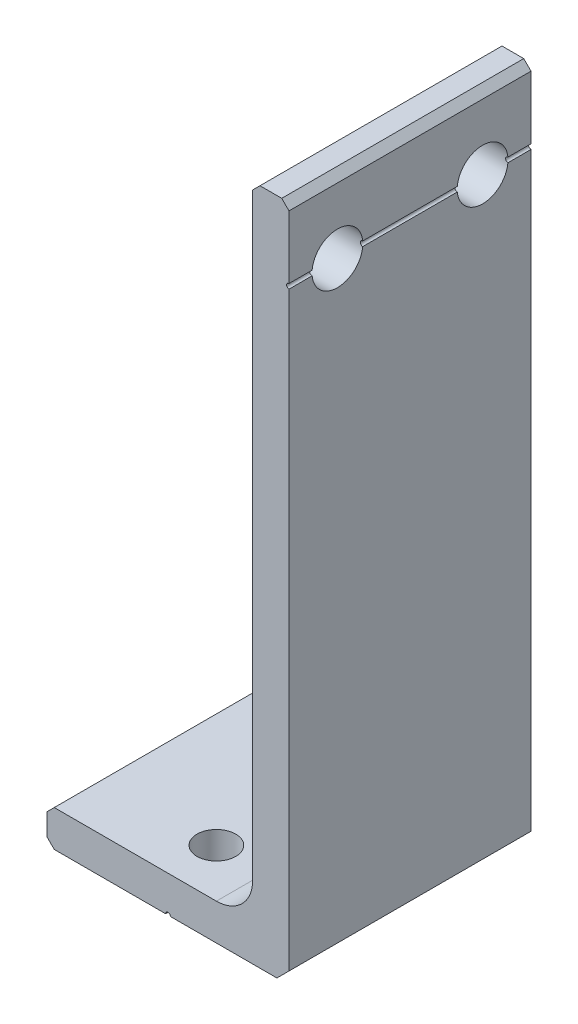
SolidWorks part; units mm, degrees
material "6061 合金"
ref_plane "前视基准面" through (0, 0, 0) normal (0, 0, 1) x (1, 0, 0)
ref_plane "上视基准面" through (0, 0, 0) normal (0, 1, 0) x (1, 0, 0)
ref_plane "右视基准面" through (0, 0, 0) normal (1, 0, 0) x (0, 0, -1)
sketch "草图1" plane through (0, 0, 0) normal (0, 0, 1) x (1, 0, 0)
  line L0 (0, 0) -> (20, 0)
  line L1 (20, 0) -> (20, 56)
  line L2 (20, 56) -> (17, 56)
  line L3 (17, 56) -> (17, 3)
  line L4 (17, 3) -> (0, 3)
  line L5 (0, 3) -> (0, 0)
  dimension "D1" = 3
  dimension "D2" = 53
  dimension "D3" = 3
  dimension "D4" = 20
extrude "凸台-拉伸1" add sketch "草图1" along normal blind 20
fillet "圆角1" radius 3 1 edges at (17, 3, 10)
sketch "草图2" plane through (17, 0, 0) normal (-1, 0, 0) x (0, 0, 1)
  line L0 (10, 0) -> (10, 56) construction
  line L1 (20, 0) -> (0, 0) construction
  line L2 (20, 56) -> (0, 56) construction
  line L3 (0, 6) -> (20, 6) construction
  circle A0 centre (4, 50) radius 2.1
  circle A1 centre (16, 50) radius 2.1
  point P10 (16, 50)
  dimension "D1" = 4.2
  dimension "D2" = 44
  dimension "D3" = 12
extrude "切除-拉伸1" cut sketch "草图2" against normal blind 20
sketch "草图3" plane through (0, 3, 0) normal (0, 1, 0) x (1, 0, 0)
  line L0 (10, 0) -> (10, -20) construction
  line L1 (14, 0) -> (0, 0) construction
  line L2 (14, -20) -> (0, -20) construction
  line L3 (0, -10) -> (14, -10) construction
  line L4 (0, -20) -> (0, 0) construction
  line L5 (14, -20) -> (14, 0) construction
  circle A0 centre (10, -4) radius 1.6
  circle A1 centre (10, -16) radius 1.6
  dimension "D1" = 10
  dimension "D2" = 3.2
  dimension "D3" = 12
extrude "切除-拉伸2" cut sketch "草图3" against normal blind 20
chamfer "倒角1" distance 1 angle 45 1 edges at (20, 0, 10)
chamfer "倒角2" distance 0.6 angle 45 4 edges at (20, 56, 10) (17, 56, 10) (0, 3, 10) (0, 0, 10)
sketch "草图4" plane through (0, 0, 20) normal (0, 0, 1) x (1, 0, 0)
  line L0 (0.6, 0) -> (19, 0) construction
  line L1 (20, 1) -> (20, 55.4) construction
  line L2 (0, 2.4) -> (0, 0.6) construction
  line L3 (19.4, 56) -> (17.6, 56) construction
  circle A0 centre (10, 0) radius 0.2
  circle A1 centre (20, 50) radius 0.2
  dimension "D1" = 0.4
  dimension "D3" = 6
  dimension "D2" = 10
extrude "切除-拉伸3" cut sketch "草图4" against normal blind 32
